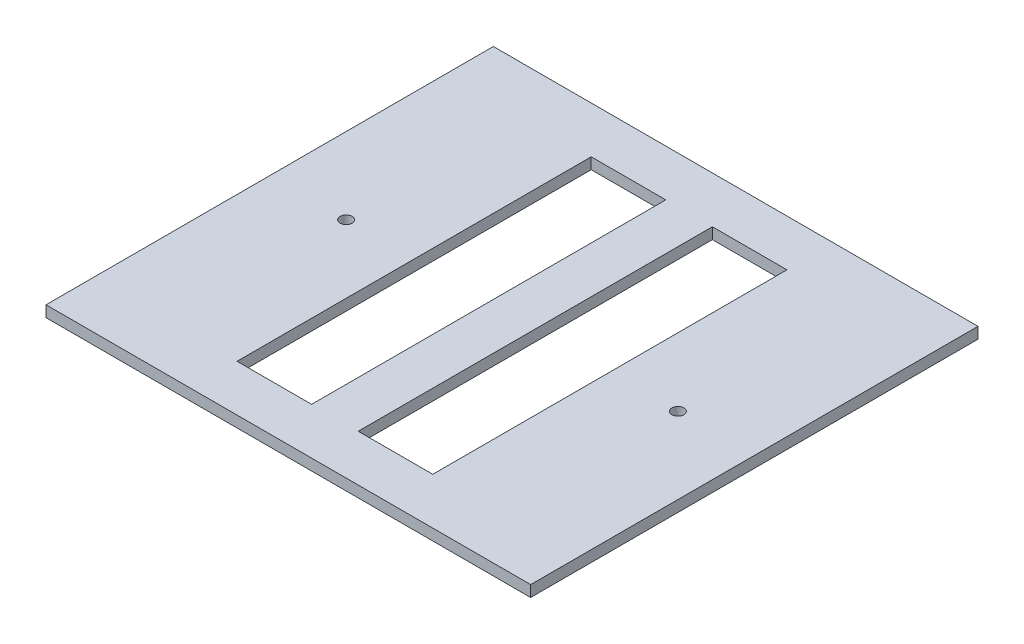
SolidWorks part; units mm, degrees
ref_plane "Front Plane" through (0, 0, 0) normal (0, 0, 1) x (1, 0, 0)
ref_plane "Top Plane" through (0, 0, 0) normal (0, 1, 0) x (1, 0, 0)
ref_plane "Right Plane" through (0, 0, 0) normal (1, 0, 0) x (0, 0, -1)
sketch "Sketch1" plane through (0, 0, 0) normal (0, 1, 0) x (1, 0, 0)
  line L1 (-65, -60) -> (65, -60)
  line L2 (-65, -60) -> (-65, 60)
  line L3 (-65, 60) -> (65, 60)
  line L4 (65, -60) -> (65, 60)
  line L5 (-65, -60) -> (65, 60) construction
  line L6 (-65, 60) -> (65, -60) construction
  point P0 (0, 0)
  dimension "D1" = 130
  dimension "D2" = 120
extrude "Boss-Extrude1" add sketch "Sketch1" along normal blind 3
sketch "Sketch2" plane through (0, 3, 0) normal (0, 1, 0) x (1, 0, 0)
  line L1 (-26.25, -47.5) -> (-6.25, -47.5)
  line L2 (-26.25, -47.5) -> (-26.25, 47.5)
  line L3 (-26.25, 47.5) -> (-6.25, 47.5)
  line L4 (-6.25, -47.5) -> (-6.25, 47.5)
  line L5 (-26.25, -47.5) -> (-6.25, 47.5) construction
  line L6 (-26.25, 47.5) -> (-6.25, -47.5) construction
  point P0 (-16.25, 0)
  dimension "D1" = 95
  dimension "D2" = 20
  dimension "D3" = 6.25
extrude "Cut-Extrude1" cut sketch "Sketch2" against normal through all both and the other way through all
mirror "Mirror1" about plane through (0, 0, 0) normal (1, 0, 0) of "Cut-Extrude1"
sketch "Sketch3" plane through (0, 3, 0) normal (0, 1, 0) x (1, 0, 0)
  circle A0 centre (44.5, 0) radius 1.6
  dimension "D1" = 3.2
  dimension "D2" = 44.5
extrude "Cut-Extrude2" cut sketch "Sketch3" against normal through all both and the other way through all
mirror "Mirror2" about plane through (0, 0, 0) normal (1, 0, 0) of "Cut-Extrude2"
